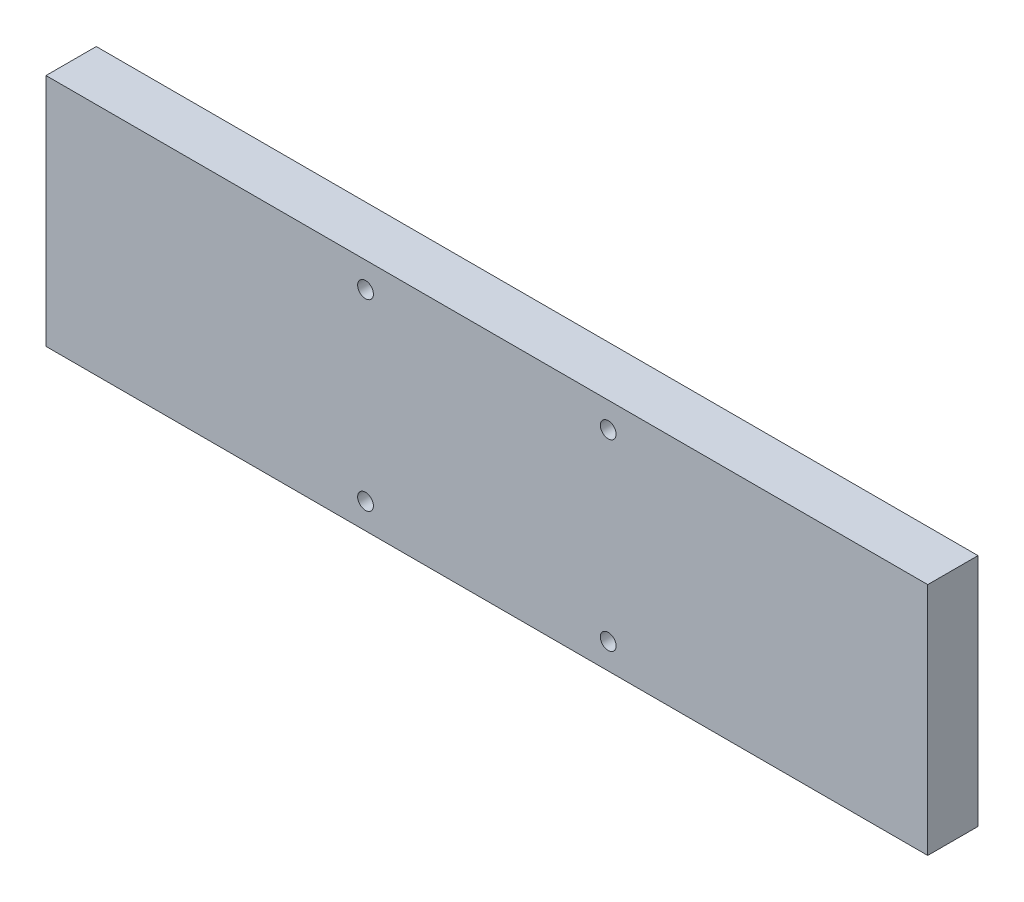
SolidWorks part; units mm, degrees
ref_plane "Front Plane" through (0, 0, 0) normal (0, 0, 1) x (1, 0, 0)
ref_plane "Top Plane" through (0, 0, 0) normal (0, 1, 0) x (1, 0, 0)
ref_plane "Right Plane" through (0, 0, 0) normal (1, 0, 0) x (0, 0, -1)
sketch "Sketch1" plane through (0, 0, 0) normal (0, 0, 1) x (1, 0, 0)
  line L1 (5029.0283, 1881.7238) -> (5356.0283, 1881.7238)
  line L2 (5029.0283, 1881.7238) -> (5029.0283, 1794.7238)
  line L3 (5029.0283, 1794.7238) -> (5356.0283, 1794.7238)
  line L4 (5356.0283, 1881.7238) -> (5356.0283, 1794.7238)
  line L5 (5029.0283, 1881.7238) -> (5356.0283, 1794.7238) construction
  line L6 (5029.0283, 1794.7238) -> (5356.0283, 1881.7238) construction
  point P4 (5192.5283, 1838.2238)
  dimension "D1" = 87
  dimension "D2" = 327
extrude "Boss-Extrude1" add sketch "Sketch1" along normal blind 18.64
sketch "GuideSketch" plane through (0, 0, 18.64) normal (0, 0, 1) x (1, 0, 0)
  line L0 (5029.0283, 1838.2238) -> (5356.0283, 1838.2238) construction
  line L1 (5029.0283, 1881.7238) -> (5029.0283, 1794.7238) construction
  line L2 (5356.0283, 1794.7238) -> (5356.0283, 1881.7238) construction
  line L3 (5192.5283, 1881.7238) -> (5192.5283, 1794.7238) construction
  line L4 (5356.0283, 1881.7238) -> (5029.0283, 1881.7238) construction
  line L5 (5029.0283, 1794.7238) -> (5356.0283, 1794.7238) construction
sketch "Sketch4" [suppressed] plane through (0, 0, 18.64) normal (0, 0, 1) x (1, 0, 0)
  line L0 (5029.0283, 1838.2238) -> (5356.0283, 1838.2238) construction
  line L1 (5117.5283, 1838.2238) -> (5267.5283, 1838.2238) construction
  line L2 (5282.5283, 1838.2238) -> (5267.5283, 1838.2238) construction
  line L3 (5102.5283, 1838.2238) -> (5117.5283, 1838.2238) construction
  line L4 (5192.5283, 1881.7238) -> (5192.5283, 1794.7238) construction
  circle A0 centre (5117.5283, 1838.2238) radius 3
  circle A1 centre (5102.5283, 1838.2238) radius 3
  circle A2 centre (5267.5283, 1838.2238) radius 3
  circle A3 centre (5282.5283, 1838.2238) radius 3
  point P11 (5192.5283, 1838.2238)
  dimension "D1" = 6
  dimension "D2" = 15
  dimension "D3" = 150
extrude "Cut-Extrude3" [suppressed] cut sketch "Sketch4" against normal through all
sketch "Sketch5" plane through (0, 0, 18.64) normal (0, 0, 1) x (1, 0, 0)
  line L0 (5147.5283, 1838.2238) -> (5237.5283, 1838.2238) construction
  line L1 (5147.5283, 1872.2238) -> (5147.5283, 1804.2238) construction
  line L2 (5237.5283, 1872.2238) -> (5237.5283, 1804.2238) construction
  line L3 (5029.0283, 1838.2238) -> (5356.0283, 1838.2238) construction
  line L4 (5192.5283, 1881.7238) -> (5192.5283, 1794.7238) construction
  circle A0 centre (5147.5283, 1872.2238) radius 2.925
  circle A1 centre (5147.5283, 1804.2238) radius 2.925
  circle A2 centre (5237.5283, 1804.2238) radius 2.925
  circle A3 centre (5237.5283, 1872.2238) radius 2.925
  point P7 (5147.5283, 1838.2238)
  point P10 (5237.5283, 1838.2238)
  point P15 (5192.5283, 1838.2238)
  dimension "D3" = 5.85
  dimension "D1" = 90
  dimension "D2" = 68
extrude "Cut-Extrude4" cut sketch "Sketch5" against normal through all
